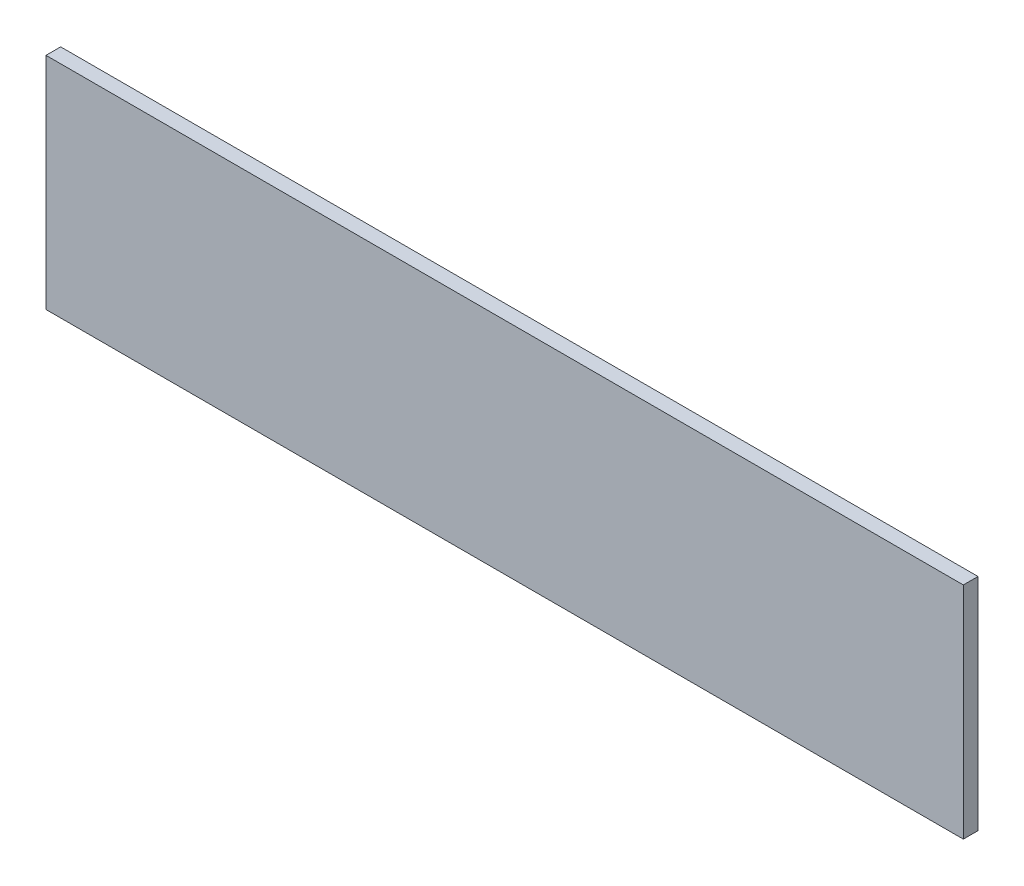
SolidWorks part; units mm, degrees
material "Pine"
ref_plane "Front Plane" through (0, 0, 0) normal (0, 0, 1) x (1, 0, 0)
ref_plane "Top Plane" through (0, 0, 0) normal (0, 1, 0) x (1, 0, 0)
ref_plane "Right Plane" through (0, 0, 0) normal (1, 0, 0) x (0, 0, -1)
sketch "Sketch1" plane through (0, 0, 0) normal (0, 0, 1) x (1, 0, 0)
  line L1 (-250, -60) -> (250, -60)
  line L2 (-250, -60) -> (-250, 60)
  line L3 (-250, 60) -> (250, 60)
  line L4 (250, -60) -> (250, 60)
  line L5 (-250, -60) -> (250, 60) construction
  line L6 (-250, 60) -> (250, -60) construction
  point P0 (0, 0)
  dimension "D1" = 500
  dimension "D2" = 120
extrude "Boss-Extrude1" add sketch "Sketch1" along normal blind 8
sketch "Sketch3" plane through (0, 0, 8) normal (0, 0, 1) x (1, 0, 0)
  line L0 (-250, 0) -> (250, 0) construction
  line L1 (-250, 60) -> (-250, -60) construction
  line L2 (250, -60) -> (250, 60) construction
  line L3 (0, 60) -> (0, -60) construction
  line L4 (250, 60) -> (-250, 60) construction
  line L5 (-250, -60) -> (250, -60) construction
  circle A0 centre (0, 0) radius 4
  circle A2 centre (-140, 0) radius 4
  circle A5 centre (140, 0) radius 4
  dimension "D1" = 8
  dimension "D3" = 8
  dimension "D6" = 140
